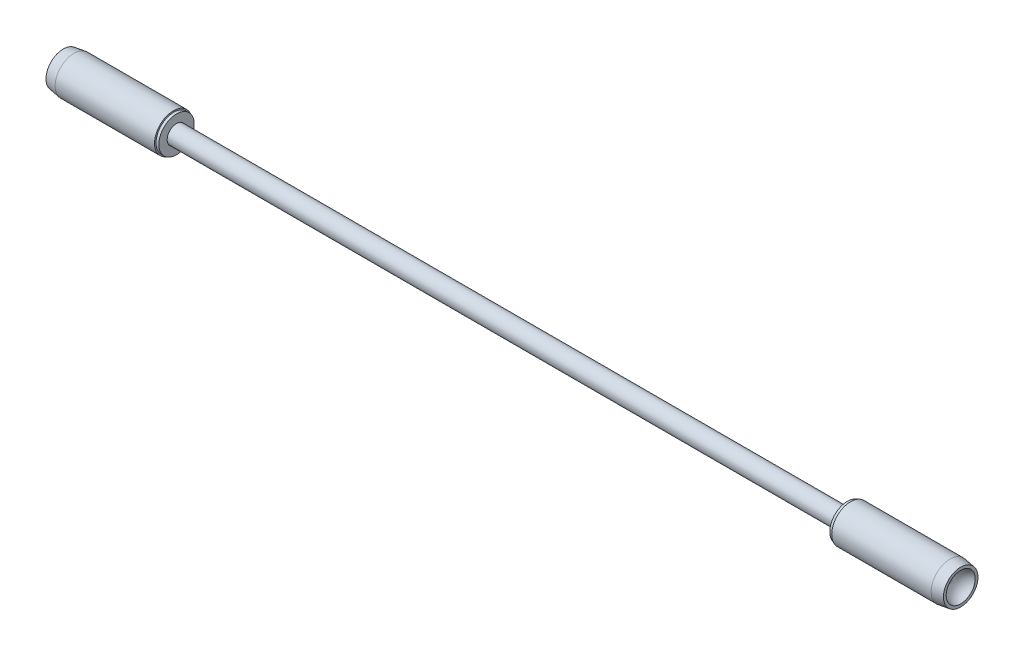
SolidWorks part; units mm, degrees
ref_plane "Front Plane" through (0, 0, 0) normal (0, 0, 1) x (1, 0, 0)
ref_plane "Top Plane" through (0, 0, 0) normal (0, 1, 0) x (1, 0, 0)
ref_plane "Right Plane" through (0, 0, 0) normal (1, 0, 0) x (0, 0, -1)
sketch "Sketch1" plane through (0, 0, 0) normal (0, 0, 1) x (1, 0, 0)
  line L0 (139.2375, 0) -> (-139.2375, 0) construction
  line L1 (-106.6375, 2.98) -> (-106.6375, 5.625)
  line L2 (-106.6375, 5.625) -> (-107.5375, 5.625)
  line L3 (-107.5375, 5.625) -> (-107.5375, 5)
  line L4 (-107.5375, 5) -> (-124.0375, 5)
  line L5 (-124.0375, 5) -> (-124.0375, 2.98)
  line L16 (-124.1375, 0) -> (-139.1375, 0)
  line L17 (-124.1375, 0) -> (-124.1375, 5)
  line L18 (-124.1375, 5) -> (-139.1375, 5)
  line L19 (-139.1375, 0) -> (-139.1375, 5)
  line L20 (-139.2375, 6) -> (-107.6375, 6)
  line L21 (-107.6375, 6) -> (-107.6375, 5.1)
  line L22 (-139.2375, 5.1) -> (-107.6375, 5.1)
  line L23 (-124.0375, 2.98) -> (-106.6375, 2.98)
  line L24 (-139.2375, 0.6919) -> (-139.2375, 5.1)
  line L25 (-139.2375, 0) -> (-139.2375, 5) construction
  line L26 (-139.2375, 0.6919) -> (-139.1375, 0.6919)
  line L27 (-124.0375, 0) -> (-124.0375, 2.93)
  line L28 (-124.0375, 2.93) -> (124.0375, 2.93)
  line L29 (0, 2.93) -> (0, 0)
  line L30 (124.0375, 0) -> (-124.0375, 0)
  line L31 (-139.2375, 6) -> (-142.6375, 5.5)
  line L32 (-142.6375, 5.5) -> (-142.6375, 4.6156)
  line L33 (142.6375, 5.5) -> (142.6375, 4.6156)
  line L34 (139.2375, 6) -> (142.6375, 5.5)
  line L35 (124.0375, 0) -> (124.0375, 2.93)
  line L36 (139.2375, 0.6919) -> (139.1375, 0.6919)
  line L37 (139.2375, 0.6919) -> (139.2375, 5.1)
  line L38 (124.0375, 2.98) -> (106.6375, 2.98)
  line L39 (139.2375, 5.1) -> (107.6375, 5.1)
  line L40 (107.6375, 6) -> (107.6375, 5.1)
  line L41 (139.2375, 6) -> (107.6375, 6)
  line L42 (139.1375, 0) -> (139.1375, 5)
  line L43 (124.1375, 5) -> (139.1375, 5)
  line L44 (124.1375, 0) -> (124.1375, 5)
  line L45 (124.1375, 0) -> (139.1375, 0)
  line L46 (124.0375, 5) -> (124.0375, 2.98)
  line L47 (107.5375, 5) -> (124.0375, 5)
  line L48 (107.5375, 5.625) -> (107.5375, 5)
  line L49 (106.6375, 5.625) -> (107.5375, 5.625)
  line L50 (106.6375, 2.98) -> (106.6375, 5.625)
  circle A0 centre (-144, 0) radius 4.7625 construction
  arc A1 (-139.2375, 0.6919) -> (-142.6375, 4.6156) centre (-144, 0) ccw
  circle A2 centre (-144, 0) radius 4.8125 construction
  circle A3 centre (144, 0) radius 4.7625 construction
  arc A4 (139.2375, 0.6919) -> (142.6375, 4.6156) centre (144, 0) cw
  dimension "D4" = 0.1
  dimension "D6" = 9.525
  dimension "D2" = 5
  dimension "D3" = 0.1
  dimension "D1" = 15
  dimension "D5" = 144
  dimension "D9" = 2.93
  dimension "D10" = 6
  dimension "D11" = 0.1
  dimension "D13" = 3.5
  dimension "D14" = 36
  dimension "D15" = 35
  dimension "D16" = 5.625
  dimension "D8" = 0.1
  dimension "D17" = 0.05
  dimension "D18" = 5.5
  dimension "D7" = 0.05
  dimension "D12" = 0.1
revolve "Revolve1" add sketch "Sketch1" angle 360 about L30
